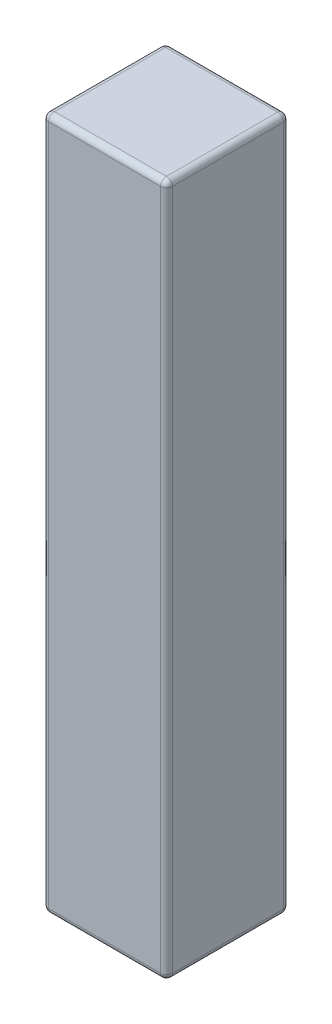
SolidWorks part; units mm, degrees
material "Plain Carbon Steel"
ref_plane "Front" through (0, 0, 0) normal (0, 0, 1) x (1, 0, 0)
ref_plane "Top" through (0, 0, 0) normal (0, 1, 0) x (1, 0, 0)
ref_plane "Right" through (0, 0, 0) normal (1, 0, 0) x (0, 0, -1)
sketch "Sketch1" plane through (0, 0, 0) normal (0, 1, 0) x (1, 0, 0)
  line L1 (-1.5875, 1.5748) -> (1.5875, 1.5748)
  line L2 (-1.5875, 1.5748) -> (-1.5875, -1.5748)
  line L3 (-1.5875, -1.5748) -> (1.5875, -1.5748)
  line L4 (1.5875, 1.5748) -> (1.5875, -1.5748)
  line L8 (0, 0) -> (1.5875, 0) construction
  line L9 (0, 0) -> (0, 1.5748) construction
  dimension "D1" = 3.175
  dimension "D2" = 3.1496
extrude "Extrude1" add sketch "Sketch1" along normal blind 17.78
fillet "Fillet1" radius 0.15 12 edges at (0, 0, 1.5748) (1.5875, 8.89, 1.5748) (1.5875, 0, 0) (-1.5875, 8.89, 1.5748) (-1.5875, 0, 0) (1.5875, 17.78, 0) (0, 17.78, 1.5748) (-1.5875, 17.78, 0) (1.5875, 8.89, -1.5748) (0, 17.78, -1.5748) (-1.5875, 8.89, -1.5748) (0, 0, -1.5748)
